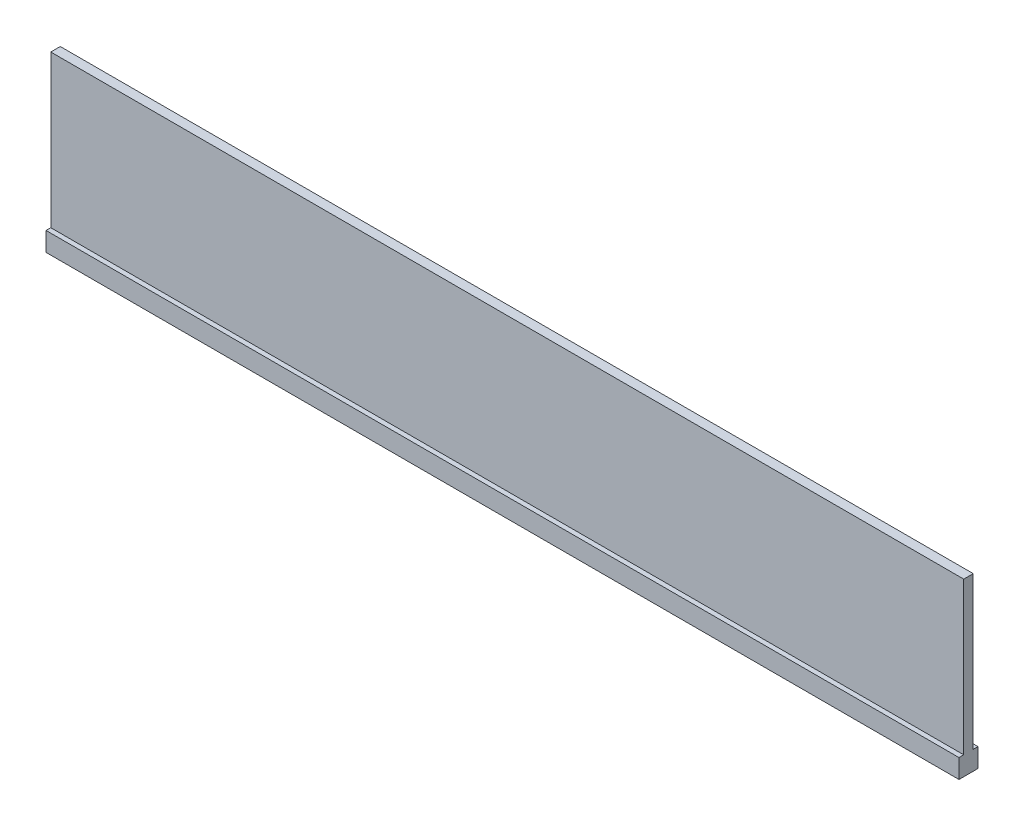
SolidWorks part; units mm, degrees
material "Nylon 6/10"
ref_plane "Front Plane" through (0, 0, 0) normal (0, 0, 1) x (1, 0, 0)
ref_plane "Top Plane" through (0, 0, 0) normal (0, 1, 0) x (1, 0, 0)
ref_plane "Right Plane" through (0, 0, 0) normal (1, 0, 0) x (0, 0, -1)
sketch "Sketch1" plane through (0, 0, 0) normal (0, 0, 1) x (1, 0, 0)
  line L1 (-91.3738, 28.9978) -> (61.0262, 28.9978)
  line L2 (-91.3738, 28.9978) -> (-91.3738, 54.3978)
  line L3 (-91.3738, 54.3978) -> (61.0262, 54.3978)
  line L4 (61.0262, 28.9978) -> (61.0262, 54.3978)
  dimension "D1" = 152.4
  dimension "D2" = 25.4
extrude "Boss-Extrude1" add sketch "Sketch1" along normal blind 1.5875
sketch "Sketch2" plane through (-91.3738, 0, 0) normal (-1, 0, 0) x (0, 0, 1)
  line L0 (0.7937, 28.9978) -> (0.7937, 30.6259) construction
  line L1 (-0.7937, 28.9978) -> (2.3812, 28.9978)
  line L2 (-0.7937, 28.9978) -> (-0.7937, 25.8228)
  line L3 (-0.7937, 25.8228) -> (2.3813, 25.8228)
  line L4 (2.3812, 28.9978) -> (2.3813, 25.8228)
  line L5 (1.5875, 28.9978) -> (0, 28.9978) construction
  line L6 (0.7937, 28.9978) -> (0.7937, 26.6748) construction
  line L7 (0.7938, 25.8228) -> (0.7938, 26.2964) construction
  point P11 (0, 0)
  point P12 (0.7937, 28.9978)
  dimension "D1" = 3.175
  dimension "D2" = 3.175
extrude "Boss-Extrude2" add sketch "Sketch2" against normal blind 152.4
